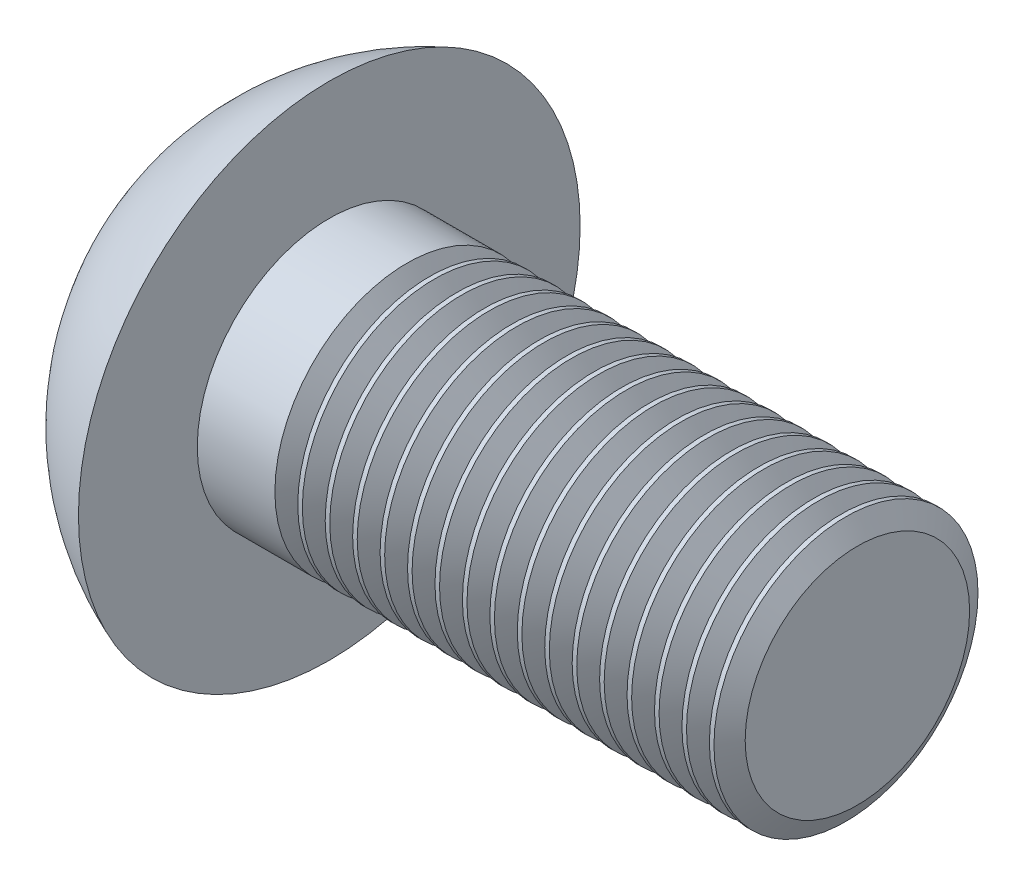
SolidWorks part; units mm, degrees
ref_plane "Front" through (0, 0, 0) normal (0, 0, 1) x (1, 0, 0)
ref_plane "Top" through (0, 0, 0) normal (0, 1, 0) x (1, 0, 0)
ref_plane "Right" through (0, 0, 0) normal (1, 0, 0) x (0, 0, -1)
sketch "Sketch1" plane through (0, 0, 0) normal (1, 0, 0) x (0, 0, -1)
  line L0 (0, 0) -> (1.6, 0) construction
  circle A0 centre (0, 0) radius 4.75
  dimension "dk" = 9.5
  dimension "a" = 1.6
extrude "BaseHead" add sketch "Sketch1" along normal blind 2.75
sketch "Sketch2" plane through (2.75, 0, 0) normal (1, 0, 0) x (0, 0, -1)
  circle A0 centre (0, 0) radius 2.5
  dimension "d" = 5
extrude "BaseBody" add sketch "Sketch2" along normal blind 10
cosmetic thread "ThreadCosmetic1" [suppressed] parameters "D1"=8.4, "THD_MINOR"=4.134
fillet "HeadFillet" [suppressed] radius 0.2
sketch "Sketch3" plane through (-13.4796, 2.4796, 0) normal (0, 0, 1) x (0, -1, 0)
  line L0 (2.4796, 13.4796) -> (2.4796, 41.0387) construction
  line L3 (-2.2704, 13.4796) -> (2.4796, 13.4796) construction
  line L5 (-7.2704, 16.2296) -> (-7.2704, 8.4796)
  line L6 (0.2596, 13.4796) -> (0.2596, 8.4796)
  line L7 (0.2596, 8.4796) -> (-7.2704, 8.4796)
  line L8 (-7.2704, 16.2296) -> (-2.2704, 16.2296)
  line L9 (-2.2704, 13.4796) -> (7.2296, 13.4796) construction
  arc A0 (-2.2704, 16.2296) -> (0.2596, 13.4796) centre (2.4796, 18.0608) ccw
  dimension "D2" = 5
  dimension "e" = 4.44
  dimension "D3" = 5
revolve "Cut-Revolve1" cut sketch "Sketch3" angle 360 about L0
sketch "Sketch4" plane through (0, 0, 0) normal (1, 0, 0) x (0, 0, -1)
  line L1 (1.7321, 0) -> (0.866, 1.5)
  line L2 (0.866, 1.5) -> (-0.866, 1.5)
  line L3 (-0.866, 1.5) -> (-1.7321, 0)
  line L4 (-1.7321, 0) -> (-0.866, -1.5)
  line L5 (-0.866, -1.5) -> (0.866, -1.5)
  line L6 (0.866, -1.5) -> (1.7321, 0)
  circle A0 centre (0, 0) radius 1.5 construction
  dimension "s" = 3
extrude "HexagonSocket" cut sketch "Sketch4" along normal blind 1.56
sketch "Sketch5" plane through (1.56, 0, 0) normal (-1, 0, 0) x (0, 0, 1)
  line L0 (0.866, -1.5) -> (-0.866, -1.5) construction
  line L1 (-0.866, -1.5) -> (-1.7321, 0) construction
  line L2 (1.7321, 0) -> (0.866, -1.5) construction
  line L3 (0.866, 1.5) -> (1.7321, 0) construction
  line L4 (-1.7321, 0) -> (-0.866, 1.5) construction
  line L5 (-0.866, 1.5) -> (0.866, 1.5) construction
  line L6 (0.866, -1.5) -> (-0.866, -1.5)
  line L7 (-0.866, -1.5) -> (-1.7321, 0)
  line L8 (1.7321, 0) -> (0.866, -1.5)
  line L9 (0.866, 1.5) -> (1.7321, 0)
  line L10 (-1.7321, 0) -> (-0.866, 1.5)
  line L11 (-0.866, 1.5) -> (0.866, 1.5)
extrude "Cut-Extrude2" cut sketch "Sketch5" against normal blind 5 draft 60
sketch "Sketch6" plane through (0, 0, 0) normal (0, 0, 1) x (1, 0, 0)
  line L0 (12.75, 2.125) -> (12.9665, 2.5)
  line L1 (12.9665, 2.5) -> (12.9665, 2.933)
  line L2 (12.9665, 2.933) -> (12.5335, 2.933)
  line L3 (12.5335, 2.933) -> (12.5335, 2.5)
  line L4 (12.5335, 2.5) -> (12.75, 2.125)
  line L5 (0, 0) -> (24.7294, 0) construction
  line L6 (12.75, -2.5) -> (12.75, 2.5) construction
  dimension "D1" = 0.433
  dimension "D2" = 5
revolve "Cut-Revolve10" cut sketch "Sketch6" angle 360 about L5
pattern_linear "LPattern10" count 17 spacing 0.5196 along (-1, 0, 0) of "Cut-Revolve10"
equation "\"D1@ThreadCosmetic1\" = \"l@BaseBody\" - \"a@Sketch1\""
equation "\"D2@Sketch6\" = \"d@Sketch2\""
equation "\"D1@Sketch6\" =  (\"d@Sketch2\" - \"THD_MINOR@ThreadCosmetic1\" )  / 2"
equation "\"D3@LPattern10\" = \"D1@Sketch6\" * 1.2"
equation "\"D1@LPattern10\" = \"D1@ThreadCosmetic1\" / \"D3@LPattern10\" + 1"
